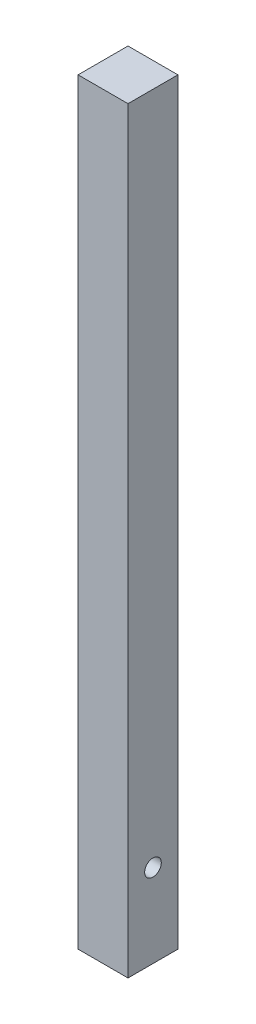
SolidWorks part; units mm, degrees
ref_plane "Alzado" through (0, 0, 0) normal (0, 0, 1) x (1, 0, 0)
ref_plane "Planta" through (0, 0, 0) normal (0, 1, 0) x (1, 0, 0)
ref_plane "Vista lateral" through (0, 0, 0) normal (1, 0, 0) x (0, 0, -1)
sketch "Croquis1" plane through (0, 0, 0) normal (0, 1, 0) x (1, 0, 0)
  line L1 (-19.05, 19.05) -> (19.05, 19.05)
  line L2 (-19.05, 19.05) -> (-19.05, -19.05)
  line L3 (-19.05, -19.05) -> (19.05, -19.05)
  line L4 (19.05, 19.05) -> (19.05, -19.05)
  line L5 (-19.05, 19.05) -> (19.05, -19.05) construction
  line L6 (-19.05, -19.05) -> (19.05, 19.05) construction
  point P0 (0, 0)
  dimension "D1" = 38.1
  dimension "D2" = 38.1
extrude "Saliente-Extruir1" add sketch "Croquis1" along normal blind 577.85
sketch "Croquis2" plane through (19.05, 0, 0) normal (1, 0, 0) x (0, 0, -1)
  line L0 (0, 0) -> (0, 63.5) construction
  circle A0 centre (0, 63.5) radius 6.35
  dimension "D2" = 12.7
  dimension "D1" = 63.5
extrude "Cortar-Extruir1" cut sketch "Croquis2" against normal blind 12.7
sketch "Croquis4" plane through (0, 0, -19.05) normal (0, 0, -1) x (-1, 0, 0)
  line L0 (0, 0) -> (0, 63.5) construction
  circle A0 centre (0, 63.5) radius 6.35
  dimension "D2" = 12.7
  dimension "D1" = 63.5
extrude "Cortar-Extruir2" cut sketch "Croquis4" against normal blind 12.6997
ref_plane "Superior" through (0, 450.85, 0) normal (0, 1, 0) x (1, 0, 0)
ref_plane "Inferior" through (0, 203.2, 0) normal (0, -1, 0) x (-1, 0, 0)
ref_plane "Medio" through (0, 336.55, 0) normal (0, 1, 0) x (1, 0, 0)
